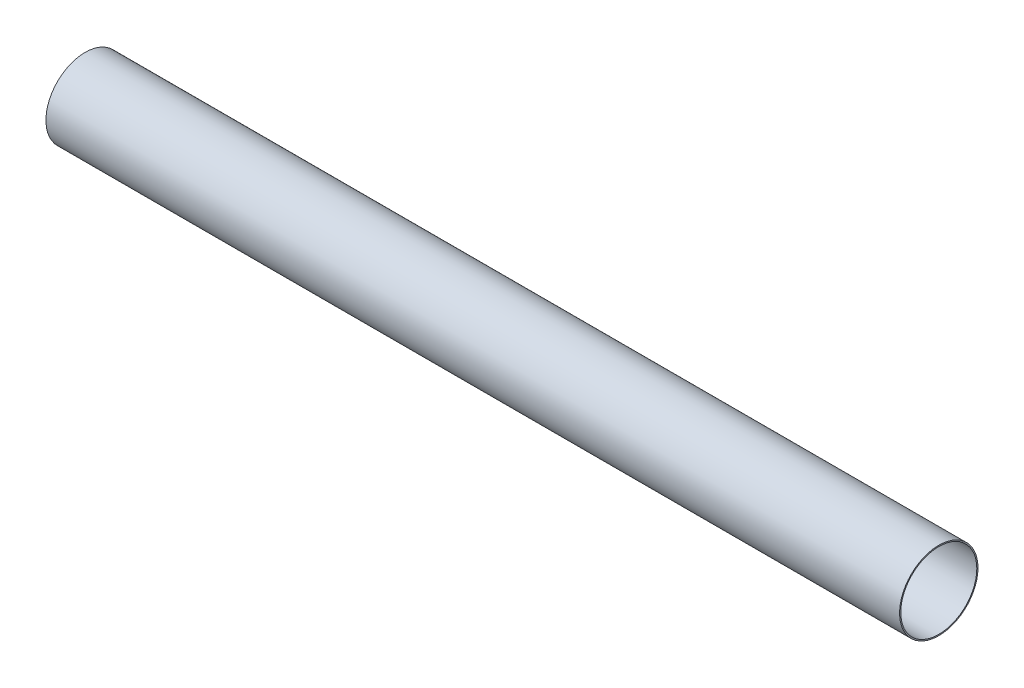
SolidWorks part; units mm, degrees
material "Natural Rubber"
ref_plane "Front Plane" through (0, 0, 0) normal (0, 0, 1) x (1, 0, 0)
ref_plane "Top Plane" through (0, 0, 0) normal (0, 1, 0) x (1, 0, 0)
ref_plane "Right Plane" through (0, 0, 0) normal (1, 0, 0) x (0, 0, -1)
sketch "Sketch1" plane through (0, 0, 0) normal (1, 0, 0) x (0, 0, -1)
  circle A0 centre (0, 0) radius 26.1937
  circle A1 centre (0, 0) radius 25.4
  dimension "D1" = 50.8
  dimension "D2" = 0.7937
extrude "Boss-Extrude1" add sketch "Sketch1" along normal mid plane 570.23
sketch "Sketch2" plane through (0, 0, 0) normal (0, 0, 1) x (1, 0, 0)
  line L0 (-285.115, 26.1938) -> (-285.115, -26.1938) construction
  line L1 (285.115, -26.1938) -> (285.115, 26.1938) construction
  circle A0 centre (-275.59, 0) radius 2.4892
  circle A1 centre (275.59, 0) radius 2.4892
  dimension "D1" = 4.9784
  dimension "D2" = 9.525
  dimension "D3" = 9.525
extrude "Cut-Extrude1" [suppressed] cut sketch "Sketch2" against normal through all both and the other way through all
sketch "Sketch3" plane through (0, 0, 0) normal (0, 1, 0) x (1, 0, 0)
  line L3 (285.115, -25.4) -> (285.115, 25.4) construction
  line L4 (-285.115, 26.1938) -> (-285.115, -26.1938) construction
  circle A0 centre (-275.59, 0) radius 2.4892
  circle A1 centre (275.59, 0) radius 2.4892
  dimension "D1" = 4.9784
  dimension "D2" = 9.525
  dimension "D3" = 9.525
extrude "Cut-Extrude2" [suppressed] cut sketch "Sketch3" against normal through all both and the other way through all
